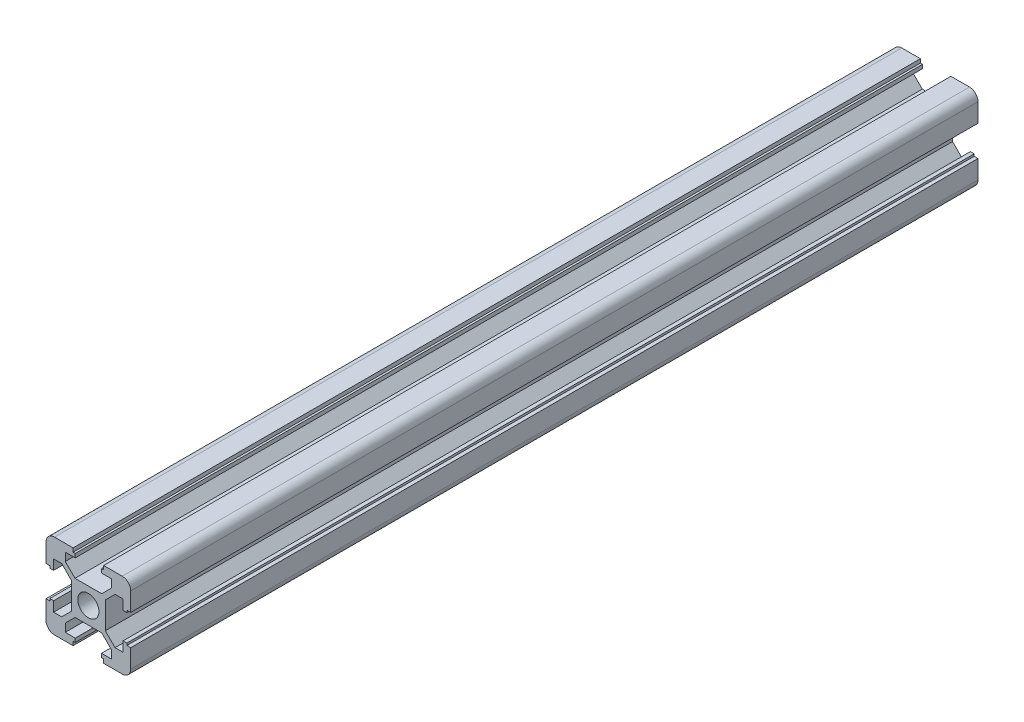
SolidWorks part; units mm, degrees
ref_plane "前视基准面" through (0, 0, 0) normal (0, 0, 1) x (1, 0, 0)
ref_plane "上视基准面" through (0, 0, 0) normal (0, 1, 0) x (1, 0, 0)
ref_plane "右视基准面" through (0, 0, 0) normal (1, 0, 0) x (0, 0, -1)
sketch "草图1" plane through (0, 0, 0) normal (0, 0, 1) x (1, 0, 0)
  line L0 (0, 0) -> (0, 12.7114) construction
  line L1 (0, 0) -> (12.7618, 0) construction
  line L2 (-3.1515, 4) -> (3.1515, 4)
  line L3 (0, 0) -> (12.1278, 12.1278) construction
  line L4 (3.1515, 4) -> (5.45, 6.2985)
  line L5 (5.45, 6.2985) -> (5.45, 8.2)
  line L6 (5.45, 8.2) -> (3.1, 8.2)
  line L7 (3.1, 8.2) -> (3.1, 9.1)
  line L8 (3.1, 9.1) -> (3.6, 9.1)
  line L9 (3.6, 9.1) -> (3.6, 10)
  line L10 (3.6, 10) -> (10, 10)
  line L11 (10, 3.6) -> (10, 10)
  line L12 (9.1, 3.6) -> (10, 3.6)
  line L13 (9.1, 3.1) -> (9.1, 3.6)
  line L14 (8.2, 3.1) -> (9.1, 3.1)
  line L15 (8.2, 5.45) -> (8.2, 3.1)
  line L16 (6.2985, 5.45) -> (8.2, 5.45)
  line L17 (4, 3.1515) -> (6.2985, 5.45)
  line L18 (4, -3.1515) -> (4, 3.1515)
  line L19 (4, -3.1515) -> (6.2985, -5.45)
  line L20 (6.2985, -5.45) -> (8.2, -5.45)
  line L21 (8.2, -5.45) -> (8.2, -3.1)
  line L22 (8.2, -3.1) -> (9.1, -3.1)
  line L23 (9.1, -3.1) -> (9.1, -3.6)
  line L24 (9.1, -3.6) -> (10, -3.6)
  line L25 (10, -3.6) -> (10, -10)
  line L26 (3.6, -10) -> (10, -10)
  line L27 (3.6, -9.1) -> (3.6, -10)
  line L28 (3.1, -9.1) -> (3.6, -9.1)
  line L29 (3.1, -8.2) -> (3.1, -9.1)
  line L30 (5.45, -8.2) -> (3.1, -8.2)
  line L31 (5.45, -6.2985) -> (5.45, -8.2)
  line L32 (3.1515, -4) -> (5.45, -6.2985)
  line L33 (-3.1515, -4) -> (3.1515, -4)
  line L34 (-3.1515, -4) -> (-5.45, -6.2985)
  line L35 (-5.45, -6.2985) -> (-5.45, -8.2)
  line L36 (-5.45, -8.2) -> (-3.1, -8.2)
  line L37 (-3.1, -8.2) -> (-3.1, -9.1)
  line L38 (-3.1, -9.1) -> (-3.6, -9.1)
  line L39 (-3.6, -9.1) -> (-3.6, -10)
  line L40 (-3.6, -10) -> (-10, -10)
  line L41 (-10, -3.6) -> (-10, -10)
  line L42 (-9.1, -3.6) -> (-10, -3.6)
  line L43 (-9.1, -3.1) -> (-9.1, -3.6)
  line L44 (-8.2, -3.1) -> (-9.1, -3.1)
  line L45 (-8.2, -5.45) -> (-8.2, -3.1)
  line L46 (-6.2985, -5.45) -> (-8.2, -5.45)
  line L47 (-4, -3.1515) -> (-6.2985, -5.45)
  line L48 (-4, -3.1515) -> (-4, 3.1515)
  line L49 (-4, 3.1515) -> (-6.2985, 5.45)
  line L50 (-6.2985, 5.45) -> (-8.2, 5.45)
  line L51 (-8.2, 5.45) -> (-8.2, 3.1)
  line L52 (-8.2, 3.1) -> (-9.1, 3.1)
  line L53 (-9.1, 3.1) -> (-9.1, 3.6)
  line L54 (-9.1, 3.6) -> (-10, 3.6)
  line L55 (-10, 3.6) -> (-10, 10)
  line L56 (-3.6, 10) -> (-10, 10)
  line L57 (-3.6, 9.1) -> (-3.6, 10)
  line L58 (-3.1, 9.1) -> (-3.6, 9.1)
  line L59 (-3.1, 8.2) -> (-3.1, 9.1)
  line L60 (-5.45, 8.2) -> (-3.1, 8.2)
  line L61 (-5.45, 6.2985) -> (-5.45, 8.2)
  line L62 (-3.1515, 4) -> (-5.45, 6.2985)
  circle A0 centre (0, 0) radius 2.5
  point P4 (10, 10)
  point P5 (-4, 0)
  point P24 (4, 0)
  point P40 (0, -4)
  point P69 (0, 4)
  point P74 (0, 0)
  dimension "D9" = 5
  dimension "D1" = 4
  dimension "D2" = 0.6
  dimension "D3" = 5.45
  dimension "D4" = 8.2
  dimension "D5" = 3.1
  dimension "D6" = 3.6
  dimension "D7" = 0.9
  dimension "D8" = 1.8
extrude "凸台-拉伸1" add sketch "草图1" along normal blind 200
fillet "圆角1" radius 2 4 edges at (10, -10, 100) (-10, -10, 100) (-10, 10, 100) (10, 10, 100)
